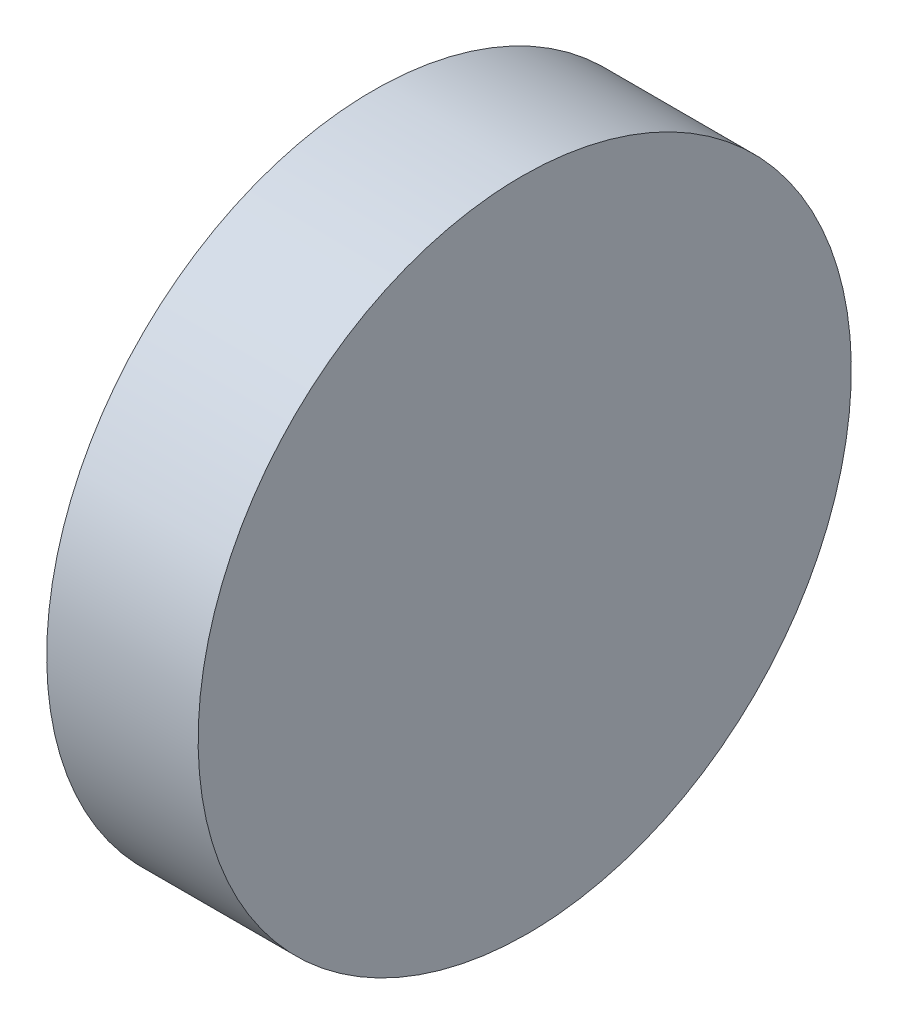
SolidWorks part; units mm, degrees
ref_plane "前视基准面" through (0, 0, 0) normal (0, 0, 1) x (1, 0, 0)
ref_plane "上视基准面" through (0, 0, 0) normal (0, 1, 0) x (1, 0, 0)
ref_plane "右视基准面" through (0, 0, 0) normal (1, 0, 0) x (0, 0, -1)
sketch "草图1" plane through (0, 0, 0) normal (0, 0, 1) x (1, 0, 0)
  line L0 (15.2768, 0) -> (-15.2768, 0) construction
  line L1 (0, 6.35) -> (0, -6.35)
  line L2 (0, -6.35) -> (3, -6.35)
  line L3 (3, -6.35) -> (2.8892, 6.35)
  line L4 (0, 6.35) -> (2.8892, 6.35)
  point P5 (0, 0)
  dimension "D1" = 3
  dimension "D2" = 12.7
  dimension "D3" = 0.5
extrude "凸台-拉伸1" add sketch "草图1" along normal blind 12.7 contours L1 L2 L3 L4
sketch "草图2" plane through (0, 0, 0) normal (-1, 0, 0) x (0, 0, 1)
  line L4 (0, 6.35) -> (0, -6.35)
  line L5 (0, -6.35) -> (12.7, -6.35)
  line L6 (12.7, -6.35) -> (12.7, 6.35)
  line L7 (12.7, 6.35) -> (0, 6.35)
  line L8 (0, 6.35) -> (0, -6.35)
  line L9 (0, -6.35) -> (12.7, -6.35)
  line L10 (12.7, -6.35) -> (12.7, 6.35)
  line L11 (12.7, 6.35) -> (0, 6.35)
  circle A0 centre (6.35, 0) radius 6.35
  point P4 (0, 0)
  point P7 (6.35, 6.35)
  line M1 (0, 6.35) -> (0, -6.35)
  line M2 (0, -6.35) -> (12.7, -6.35)
  line M3 (12.7, -6.35) -> (12.7, 6.35)
  line M4 (12.7, 6.35) -> (0, 6.35)
  dimension "D2" = 12.7
  dimension "D1" = 0
extrude "切除-拉伸1" cut sketch "草图2" against normal blind 10 contours A0 L8 M2 | A0 L9 M3 | A0 L10 M4 | A0 L11 M1
